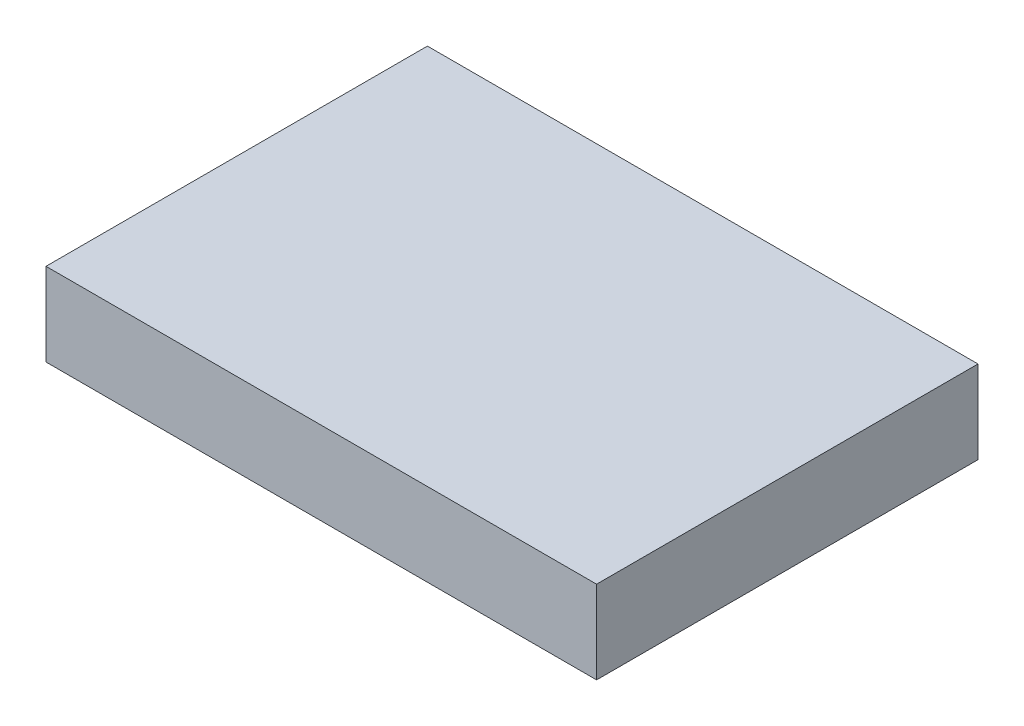
SolidWorks part; units mm, degrees
ref_plane "Front Plane" through (0, 0, 0) normal (0, 0, 1) x (1, 0, 0)
ref_plane "Top Plane" through (0, 0, 0) normal (0, 1, 0) x (1, 0, 0)
ref_plane "Right Plane" through (0, 0, 0) normal (1, 0, 0) x (0, 0, -1)
sketch "Sketch1" plane through (0, 0, 0) normal (0, 1, 0) x (1, 0, 0)
  line L1 (-105.41, -73.025) -> (105.41, -73.025)
  line L2 (-105.41, -73.025) -> (-105.41, 73.025)
  line L3 (-105.41, 73.025) -> (105.41, 73.025)
  line L4 (105.41, -73.025) -> (105.41, 73.025)
  line L5 (-105.41, -73.025) -> (105.41, 73.025) construction
  line L6 (-105.41, 73.025) -> (105.41, -73.025) construction
  point P0 (0, 0)
  dimension "D1" = 210.82
  dimension "D2" = 146.05
extrude "Boss-Extrude1" add sketch "Sketch1" along normal blind 31.75
shell "Shell1" thickness 3.048
